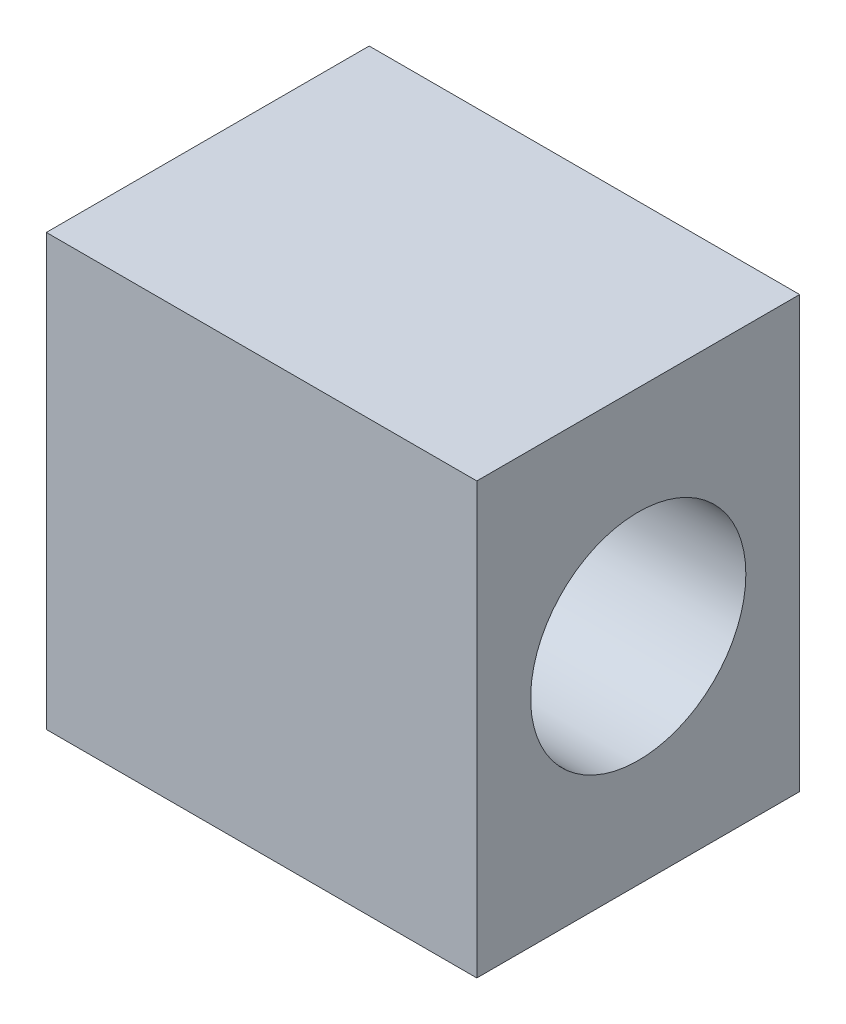
SolidWorks part; units mm, degrees
ref_plane "Front Plane" through (0, 0, 0) normal (0, 0, 1) x (1, 0, 0)
ref_plane "Top Plane" through (0, 0, 0) normal (0, 1, 0) x (1, 0, 0)
ref_plane "Right Plane" through (0, 0, 0) normal (1, 0, 0) x (0, 0, -1)
sketch "Sketch3" plane through (0, 0, 0) normal (0, 1, 0) x (1, 0, 0)
  line L0 (-10, 0) -> (10, 0) construction
  line L1 (0, 7.5) -> (0, -7.5) construction
  line L2 (-10, 7.5) -> (-10, -7.5)
  line L3 (-10, -7.5) -> (10, -7.5)
  line L4 (10, -7.5) -> (10, 7.5)
  line L5 (-10, 7.5) -> (10, 7.5)
  point P4 (0, 0)
  point P8 (0, 0)
  point P11 (-10, 0)
  point P16 (-10, 7.5)
  dimension "D1" = 15
  dimension "D2" = 20
extrude "Boss-Extrude1" add sketch "Sketch3" along normal blind 20
sketch "Sketch5" plane through (10, 0, 0) normal (1, 0, 0) x (0, 0, -1)
  circle A1 centre (0, 10) radius 5
extrude "Cut-Extrude1" cut sketch "Sketch5" against normal blind 10
sketch "Sketch6" plane through (-10, 0, 0) normal (-1, 0, 0) x (0, 0, 1)
  circle A0 centre (0, 10) radius 5
sketch "Sketch7" plane through (0, 0, 0) normal (0, -1, 0) x (1, 0, 0)
  circle A0 centre (0, 0) radius 5
extrude "Cut-Extrude6" cut sketch "Sketch7" against normal blind 4 contours A0
